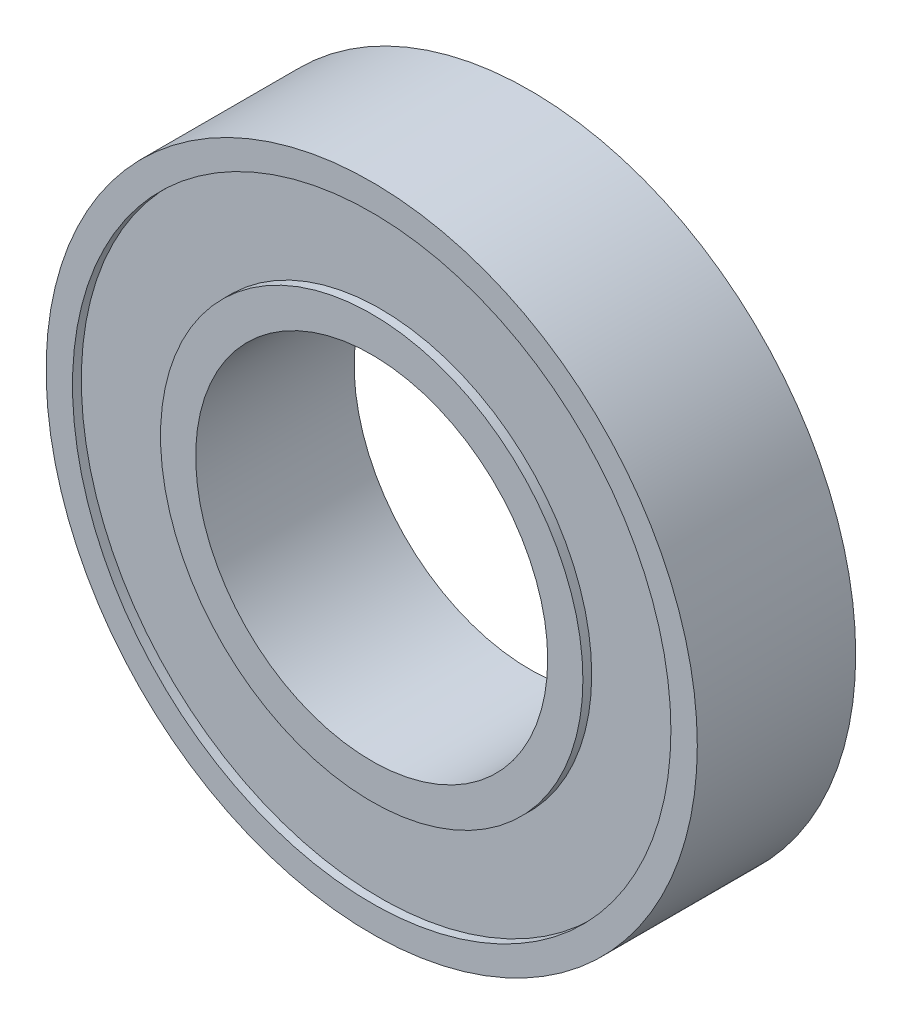
SolidWorks part; units mm, degrees
material "AISI 304"
ref_plane "前基準面" through (0, 0, 0) normal (0, 0, 1) x (1, 0, 0)
ref_plane "上基準面" through (0, 0, 0) normal (0, 1, 0) x (1, 0, 0)
ref_plane "右基準面" through (0, 0, 0) normal (1, 0, 0) x (0, 0, -1)
sketch "草圖1" plane through (0, 0, 0) normal (0, 0, 1) x (1, 0, 0)
  circle A0 centre (0, 0) radius 18.5
  dimension "D1" = 37
extrude "填料-伸長1" add sketch "草圖1" along normal mid plane 9
sketch "草圖2" plane through (0, 0, 4.5) normal (0, 0, 1) x (1, 0, 0)
  circle A0 centre (0, 0) radius 10
  dimension "D1" = 20
extrude "除料-伸長1" cut sketch "草圖2" against normal through all
sketch "草圖3" plane through (0, 0, 4.5) normal (0, 0, 1) x (1, 0, 0)
  circle A0 centre (0, 0) radius 17
  circle A1 centre (0, 0) radius 12
  dimension "D1" = 34
  dimension "D2" = 24
extrude "除料-伸長2" cut sketch "草圖3" against normal blind 0.5
mirror "鏡射1" about plane through (0, 0, 0) normal (0, 0, 1) of "除料-伸長2"
